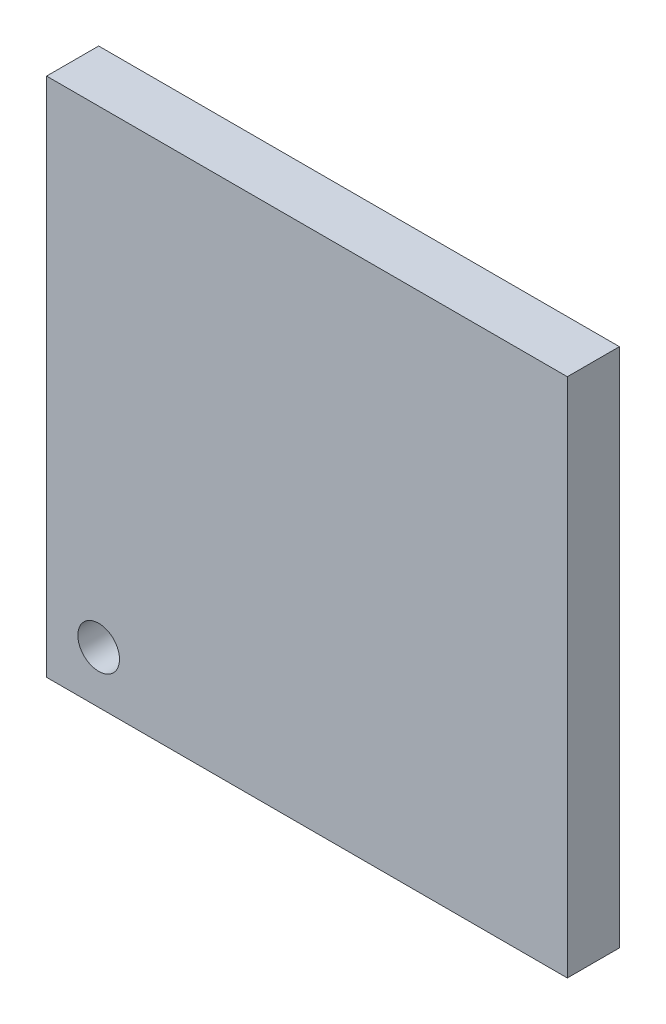
SolidWorks part; units mm, degrees
ref_plane "Přední rovina" through (0, 0, 0) normal (0, 0, 1) x (1, 0, 0)
ref_plane "Vrchní rovina" through (0, 0, 0) normal (0, 1, 0) x (1, 0, 0)
ref_plane "Pravá rovina" through (0, 0, 0) normal (1, 0, 0) x (0, 0, -1)
sketch "Skica1" plane through (0, 0, 0) normal (0, 0, 1) x (1, 0, 0)
  line L1 (50, 50) -> (-50, 50)
  line L2 (50, 50) -> (50, -50)
  line L3 (50, -50) -> (-50, -50)
  line L4 (-50, 50) -> (-50, -50)
  line L5 (50, 50) -> (-50, -50) construction
  line L6 (50, -50) -> (-50, 50) construction
  point P0 (0, 0)
  dimension "D1" = 100
  dimension "D2" = 100
extrude "Přidat vysunutím1" add sketch "Skica1" along normal blind 10
sketch "Skica3" plane through (0, 0, 10) normal (0, 0, 1) x (1, 0, 0)
  line L0 (-50, 50) -> (-50, -50) construction
  line L1 (-50, -50) -> (50, -50) construction
  circle A0 centre (-40, -40) radius 4
  point P6 (-19.6872, -50)
  dimension "D1" = 8
  dimension "D2" = 10
  dimension "D3" = 10
extrude "Odebrat vysunutím1" cut sketch "Skica3" against normal up to next contours A0
